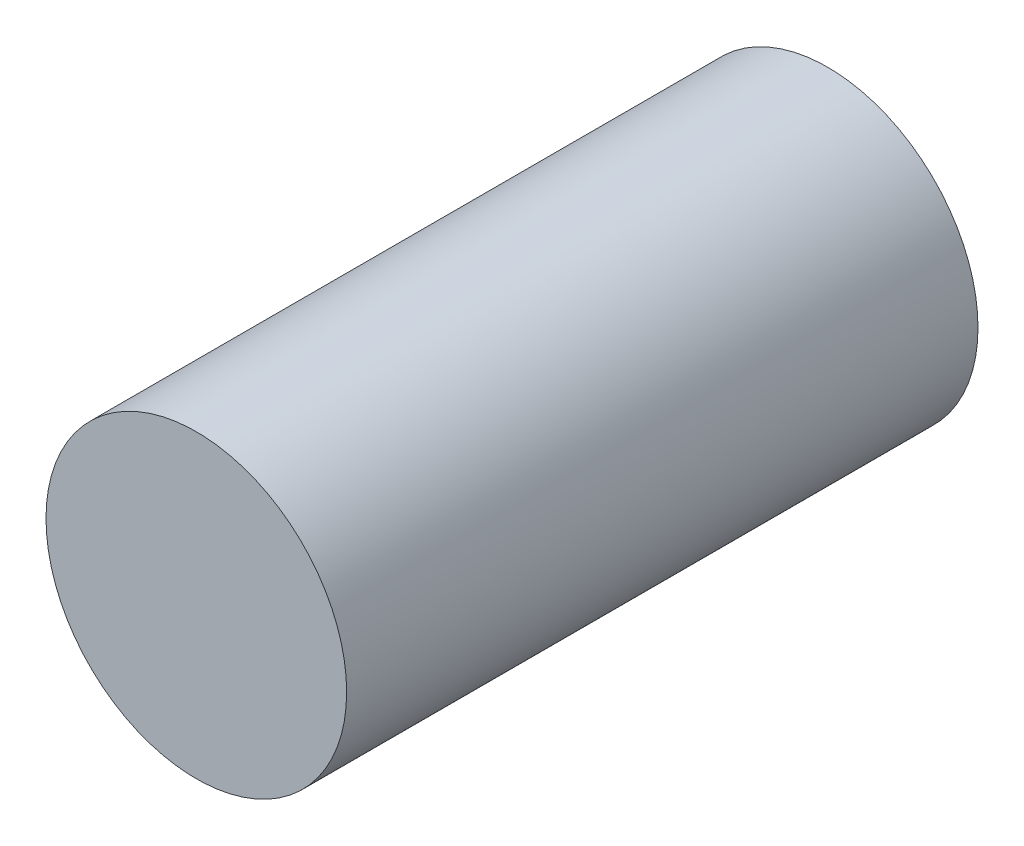
SolidWorks part; units mm, degrees
ref_plane "前视基准面" through (0, 0, 0) normal (0, 0, 1) x (1, 0, 0)
ref_plane "上视基准面" through (0, 0, 0) normal (0, 1, 0) x (1, 0, 0)
ref_plane "右视基准面" through (0, 0, 0) normal (1, 0, 0) x (0, 0, -1)
sketch "草图1" plane through (0, 0, 0) normal (0, 0, 1) x (1, 0, 0)
  circle A0 centre (-6.4015, -1.5829) radius 0.15
extrude "凸台-拉伸1" add sketch "草图1" along normal blind 0.75
sketch "草图2" plane through (0, 0, 0) normal (0, 0, -1) x (-1, 0, 0)
  circle A0 centre (6.396, -1.6126) radius 0.3018
extrude "切除-拉伸1" cut sketch "草图2" against normal blind 0.12
